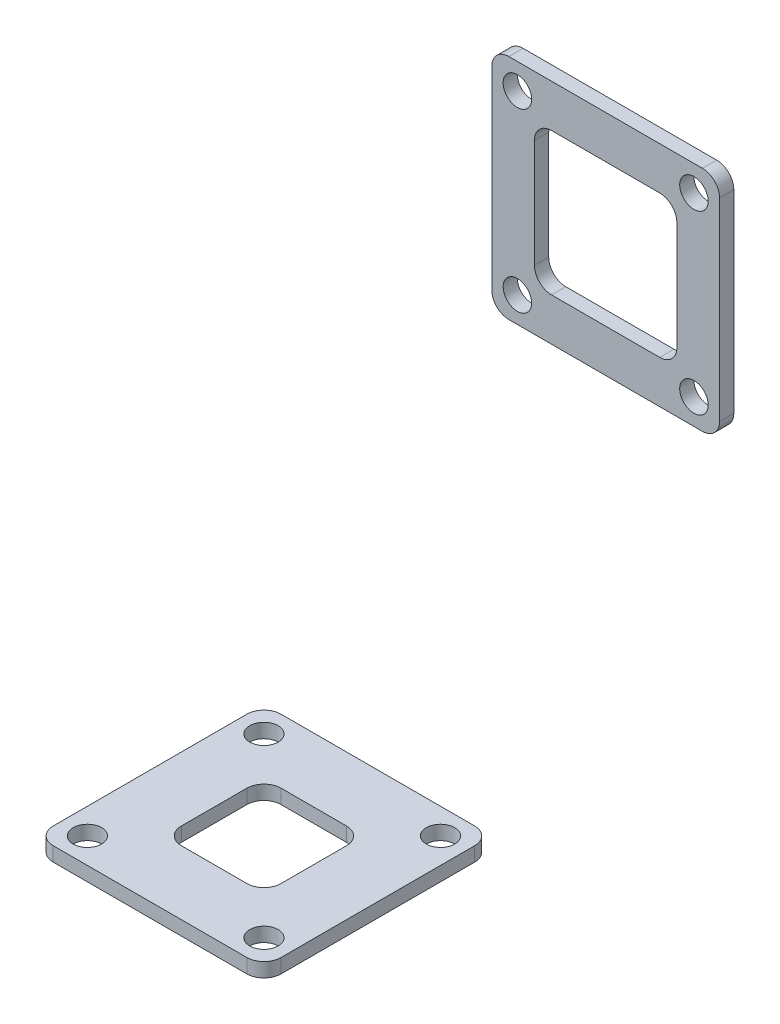
SolidWorks part; units mm, degrees
ref_plane "Front" through (0, 0, 0) normal (0, 0, 1) x (1, 0, 0)
ref_plane "Top" through (0, 0, 0) normal (0, 1, 0) x (1, 0, 0)
ref_plane "Right" through (0, 0, 0) normal (1, 0, 0) x (0, 0, -1)
sketch "Sketch1" plane through (0, 0, 0) normal (0, 0, 1) x (1, 0, 0)
  line L0 (0, 0) -> (0, 76.2) construction
  line L1 (-21.59, 101.6) -> (21.59, 101.6)
  line L2 (-25.4, 97.79) -> (-25.4, 54.61)
  line L3 (-21.59, 50.8) -> (21.59, 50.8)
  line L4 (25.4, 97.79) -> (25.4, 54.61)
  line L5 (-25.4, 101.6) -> (25.4, 50.8) construction
  line L6 (-25.4, 50.8) -> (25.4, 101.6) construction
  line L7 (-12.065, 92.075) -> (12.065, 92.075)
  line L8 (-15.875, 88.265) -> (-15.875, 64.135)
  line L9 (-12.065, 60.325) -> (12.065, 60.325)
  line L10 (15.875, 88.265) -> (15.875, 64.135)
  line L11 (-15.875, 92.075) -> (15.875, 60.325) construction
  line L12 (-15.875, 60.325) -> (15.875, 92.075) construction
  line L13 (-19.685, 95.885) -> (19.685, 95.885) construction
  line L14 (19.685, 95.885) -> (19.685, 56.515) construction
  line L15 (19.685, 56.515) -> (-19.685, 56.515) construction
  line L16 (-19.685, 56.515) -> (-19.685, 95.885) construction
  arc A0 (21.59, 101.6) -> (25.4, 97.79) centre (21.59, 97.79) cw
  arc A1 (21.59, 50.8) -> (25.4, 54.61) centre (21.59, 54.61) ccw
  arc A2 (-25.4, 54.61) -> (-21.59, 50.8) centre (-21.59, 54.61) ccw
  arc A3 (-21.59, 101.6) -> (-25.4, 97.79) centre (-21.59, 97.79) ccw
  arc A4 (12.065, 60.325) -> (15.875, 64.135) centre (12.065, 64.135) ccw
  arc A5 (-15.875, 64.135) -> (-12.065, 60.325) centre (-12.065, 64.135) ccw
  arc A6 (12.065, 92.075) -> (15.875, 88.265) centre (12.065, 88.265) cw
  arc A7 (-12.065, 92.075) -> (-15.875, 88.265) centre (-12.065, 88.265) ccw
  circle A8 centre (-19.685, 95.885) radius 3.175
  circle A9 centre (19.685, 95.885) radius 3.175
  circle A10 centre (-19.685, 56.515) radius 3.175
  circle A11 centre (19.685, 56.515) radius 3.175
  point P39 (0, 76.2)
  point P46 (0, 95.885)
  point P47 (0, 101.6)
  point P49 (-19.685, 76.2)
  point P50 (-25.4, 76.2)
  dimension "D3" = 3.81
  dimension "D5" = 39.37
  dimension "D6" = 6.35
  dimension "D1" = 50.8
  dimension "D2" = 31.75
  dimension "D4" = 76.2
extrude "Top-Flange" add sketch "Sketch1" against normal blind 3.175 contours L1 A0 L4 A1 L3 A2 L2 A3
sketch "Sketch2" plane through (0, 0, 0) normal (0, 1, 0) x (1, 0, 0)
  line L0 (0, 0) -> (0, -76.2) construction
  line L1 (-21.59, -50.8) -> (21.59, -50.8)
  line L2 (-25.4, -54.61) -> (-25.4, -97.79)
  line L3 (-21.59, -101.6) -> (21.59, -101.6)
  line L4 (25.4, -54.61) -> (25.4, -97.79)
  line L5 (-25.4, -50.8) -> (25.4, -101.6) construction
  line L6 (-25.4, -101.6) -> (25.4, -50.8) construction
  line L7 (-7.3025, -65.0875) -> (7.3025, -65.0875)
  line L8 (-11.1125, -68.8975) -> (-11.1125, -83.5025)
  line L9 (-7.3025, -87.3125) -> (7.3025, -87.3125)
  line L10 (11.1125, -68.8975) -> (11.1125, -83.5025)
  line L11 (-11.1125, -65.0875) -> (11.1125, -87.3125) construction
  line L12 (-11.1125, -87.3125) -> (11.1125, -65.0875) construction
  line L13 (-19.685, -56.515) -> (-19.685, -95.885) construction
  line L14 (-19.685, -95.885) -> (19.685, -95.885) construction
  line L15 (19.685, -95.885) -> (19.685, -56.515) construction
  line L16 (19.685, -56.515) -> (-19.685, -56.515) construction
  arc A0 (7.3025, -65.0875) -> (11.1125, -68.8975) centre (7.3025, -68.8975) cw
  arc A1 (7.3025, -87.3125) -> (11.1125, -83.5025) centre (7.3025, -83.5025) ccw
  arc A2 (-11.1125, -83.5025) -> (-7.3025, -87.3125) centre (-7.3025, -83.5025) ccw
  arc A3 (-25.4, -97.79) -> (-21.59, -101.6) centre (-21.59, -97.79) ccw
  arc A4 (21.59, -101.6) -> (25.4, -97.79) centre (21.59, -97.79) ccw
  arc A5 (21.59, -50.8) -> (25.4, -54.61) centre (21.59, -54.61) cw
  arc A6 (-7.3025, -65.0875) -> (-11.1125, -68.8975) centre (-7.3025, -68.8975) ccw
  arc A7 (-21.59, -50.8) -> (-25.4, -54.61) centre (-21.59, -54.61) ccw
  circle A8 centre (-19.685, -56.515) radius 3.175
  circle A9 centre (19.685, -56.515) radius 3.175
  circle A10 centre (-19.685, -95.885) radius 3.175
  circle A11 centre (19.685, -95.885) radius 3.175
  point P0 (0, -76.2)
  point P5 (0, -76.2)
  dimension "D5" = 3.81
  dimension "D3" = 6.35
  dimension "D1" = 50.8
  dimension "D2" = 22.225
  dimension "D4" = 76.2
  dimension "D6" = 39.37
extrude "Bottom-Flange" add sketch "Sketch2" against normal blind 3.175 separate body contours L1 A5 L4 A4 L3 A3 L2 A7
